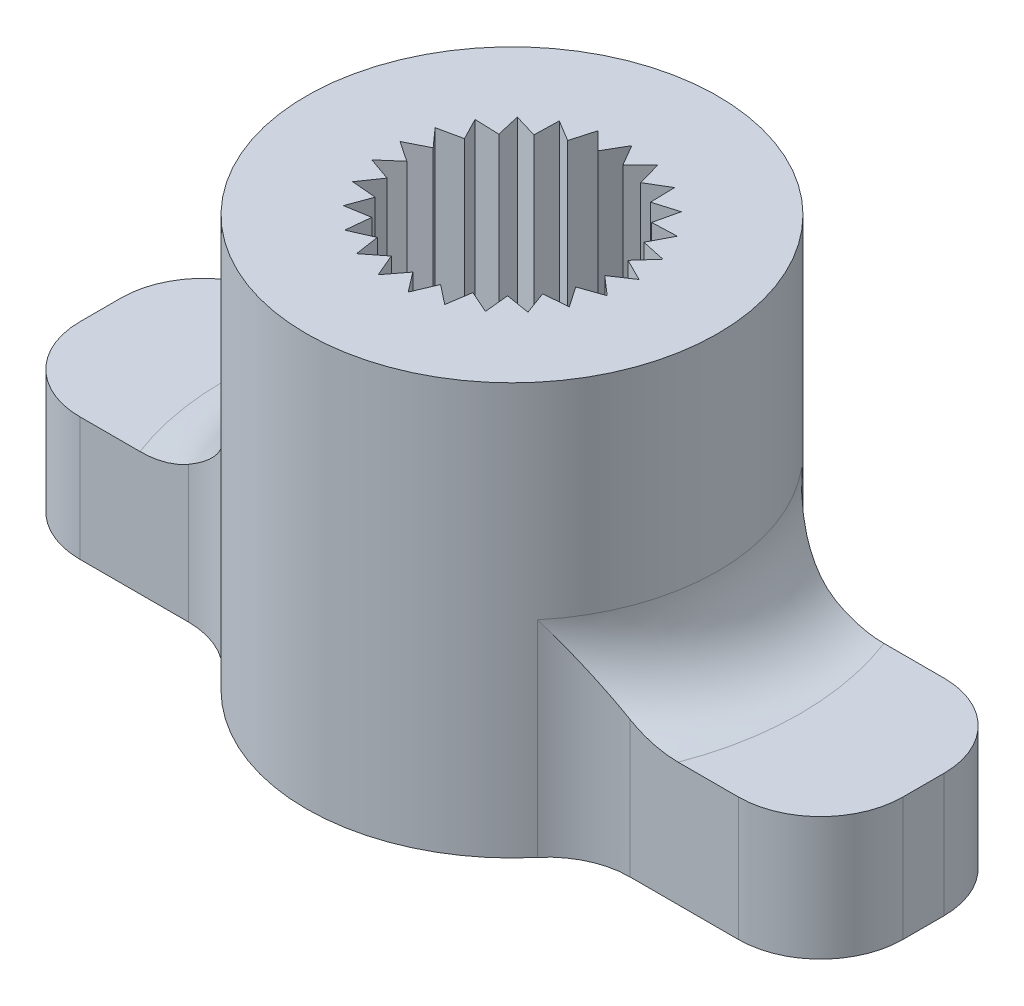
SolidWorks part; units mm, degrees
ref_plane "Front Plane" through (0, 0, 0) normal (0, 0, 1) x (1, 0, 0)
ref_plane "Top Plane" through (0, 0, 0) normal (0, 1, 0) x (1, 0, 0)
ref_plane "Right Plane" through (0, 0, 0) normal (1, 0, 0) x (0, 0, -1)
sketch "Sketch3" plane through (0, 0, 0) normal (0, 1, 0) x (1, 0, 0)
  circle A0 centre (0, 0) radius 5
  dimension "D1" = 10
extrude "Boss-Extrude1" add sketch "Sketch3" along normal blind 10
sketch "Sketch4" plane through (0, 0, 0) normal (0, -1, 0) x (1, 0, 0)
  line L1 (-10, -2.5) -> (10, -2.5)
  line L2 (-10, -2.5) -> (-10, 2.5)
  line L3 (-10, 2.5) -> (10, 2.5)
  line L4 (10, -2.5) -> (10, 2.5)
  line L5 (-10, -2.5) -> (10, 2.5) construction
  line L6 (-10, 2.5) -> (10, -2.5) construction
  point P0 (0, 0)
  dimension "D1" = 20
  dimension "D2" = 5
extrude "Boss-Extrude2" add sketch "Sketch4" against normal blind 3
sketch "Sketch2" plane through (0, 0, 0) normal (0, 1, 0) x (1, 0, 0)
  line L0 (-0.3021, 2.391) -> (0, 2.91)
  line L1 (0, 2.91) -> (0.3021, 2.391)
  line L2 (0.7237, 2.8186) -> (0.8872, 2.2408)
  line L3 (0.3021, 2.391) -> (0.7237, 2.8186)
  line L4 (1.4019, 2.5501) -> (1.4166, 1.9497)
  line L5 (0.8872, 2.2408) -> (1.4019, 2.5501)
  line L6 (1.992, 2.1213) -> (1.8569, 1.5362)
  line L7 (1.4166, 1.9497) -> (1.992, 2.1213)
  line L8 (2.457, 1.5593) -> (2.1806, 1.0261)
  line L9 (1.8569, 1.5362) -> (2.457, 1.5593)
  line L10 (2.7676, 0.8992) -> (2.3673, 0.4516)
  line L11 (2.1806, 1.0261) -> (2.7676, 0.8992)
  line L12 (2.9043, 0.1827) -> (2.4052, -0.1513)
  line L13 (2.3673, 0.4516) -> (2.9043, 0.1827)
  line L14 (2.8585, -0.5453) -> (2.292, -0.7447)
  line L15 (2.4052, -0.1513) -> (2.8585, -0.5453)
  line L16 (2.633, -1.239) -> (2.0348, -1.2913)
  line L17 (2.292, -0.7447) -> (2.633, -1.239)
  line L18 (2.2422, -1.8549) -> (1.6498, -1.7568)
  line L19 (2.0348, -1.2913) -> (2.2422, -1.8549)
  line L20 (1.7105, -2.3542) -> (1.161, -2.1119)
  line L21 (1.6498, -1.7568) -> (1.7105, -2.3542)
  line L22 (1.0712, -2.7056) -> (0.5993, -2.3343)
  line L23 (1.161, -2.1119) -> (1.0712, -2.7056)
  line L24 (0.3647, -2.8871) -> (0, -2.41)
  line L25 (0.5993, -2.3343) -> (0.3647, -2.8871)
  line L26 (-0.3647, -2.8871) -> (-0.5993, -2.3343)
  line L27 (0, -2.41) -> (-0.3647, -2.8871)
  line L28 (-1.0712, -2.7056) -> (-1.161, -2.1119)
  line L29 (-0.5993, -2.3343) -> (-1.0712, -2.7056)
  line L30 (-1.7105, -2.3542) -> (-1.6498, -1.7568)
  line L31 (-1.161, -2.1119) -> (-1.7105, -2.3542)
  line L32 (-2.2422, -1.8549) -> (-2.0348, -1.2913)
  line L33 (-1.6498, -1.7568) -> (-2.2422, -1.8549)
  line L34 (-2.633, -1.239) -> (-2.292, -0.7447)
  line L35 (-2.0348, -1.2913) -> (-2.633, -1.239)
  line L36 (-2.8585, -0.5453) -> (-2.4052, -0.1513)
  line L37 (-2.292, -0.7447) -> (-2.8585, -0.5453)
  line L38 (-2.9043, 0.1827) -> (-2.3673, 0.4516)
  line L39 (-2.4052, -0.1513) -> (-2.9043, 0.1827)
  line L40 (-2.7676, 0.8992) -> (-2.1806, 1.0261)
  line L41 (-2.3673, 0.4516) -> (-2.7676, 0.8992)
  line L42 (-2.457, 1.5593) -> (-1.8569, 1.5362)
  line L43 (-2.1806, 1.0261) -> (-2.457, 1.5593)
  line L44 (-1.992, 2.1213) -> (-1.4166, 1.9497)
  line L45 (-1.8569, 1.5362) -> (-1.992, 2.1213)
  line L46 (-1.4019, 2.5501) -> (-0.8872, 2.2408)
  line L47 (-1.4166, 1.9497) -> (-1.4019, 2.5501)
  line L48 (-0.7237, 2.8186) -> (-0.3021, 2.391)
  line L49 (-0.8872, 2.2408) -> (-0.7237, 2.8186)
  line L50 (0, 2.91) -> (0, 2.41) construction
  circle A0 centre (0, 0) radius 2.41 construction
  circle A1 centre (0, 0) radius 2.91 construction
  point P80 (0, 0)
  dimension "D3" = 0.5
  dimension "D2" = 5.82
  dimension "D1" = 25
extrude "Cut-Extrude1" cut sketch "Sketch2" along normal through all
fillet "Fillet2" radius 2 10 edges at (4.3301, 1.5, -2.5) (-4.3301, 1.5, -2.5) (-10, 1.5, -2.5) (-10, 1.5, 2.5) (-4.3301, 1.5, 2.5) (4.3301, 1.5, 2.5) (10, 1.5, -2.5) (10, 1.5, 2.5) (5, 3, 0) (-5, 3, 0)
